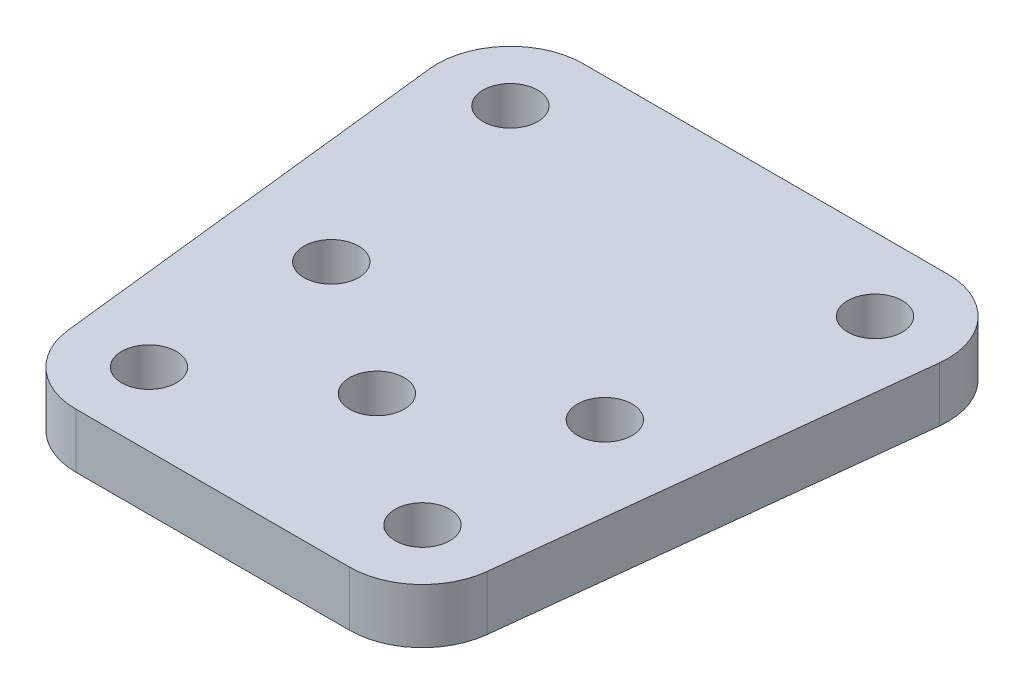
SolidWorks part; units mm, degrees
ref_plane "Front Plane" through (0, 0, 0) normal (0, 0, 1) x (1, 0, 0)
ref_plane "Top Plane" through (0, 0, 0) normal (0, 1, 0) x (1, 0, 0)
ref_plane "Right Plane" through (0, 0, 0) normal (1, 0, 0) x (0, 0, -1)
sketch "Sketch1" plane through (0, 0, 0) normal (0, 1, 0) x (1, 0, 0)
  line L8 (-10.4587, 9.3378) -> (-7.9587, -12.9827)
  line L13 (-3.9836, -16.5375) -> (11.0164, -16.5375)
  line L14 (14.9915, -12.9827) -> (17.4915, 9.3378)
  line L15 (13.5164, 13.7831) -> (-6.4836, 13.7831)
  arc A28 (-7.9587, -12.9827) -> (-3.9836, -16.5375) centre (-3.9836, -12.5375) ccw
  arc A29 (11.0164, -16.5375) -> (14.9915, -12.9827) centre (11.0164, -12.5375) ccw
  arc A30 (17.4915, 9.3378) -> (13.5164, 13.7831) centre (13.5164, 9.7831) ccw
  arc A31 (-6.4836, 13.7831) -> (-10.4587, 9.3378) centre (-6.4836, 9.7831) ccw
  circle A32 centre (-3.9836, -12.5375) radius 1.5
  circle A33 centre (11.0164, -12.5375) radius 1.5
  circle A34 centre (3.5164, -7.5375) radius 1.5
  circle A35 centre (11.0164, -2.5375) radius 1.5
  circle A36 centre (-3.9836, -2.5375) radius 1.5
  circle A37 centre (13.5164, 9.7831) radius 1.5
  circle A38 centre (-6.4836, 9.7831) radius 1.5
extrude "Boss-Extrude1" add sketch "Sketch1" along normal blind 3
